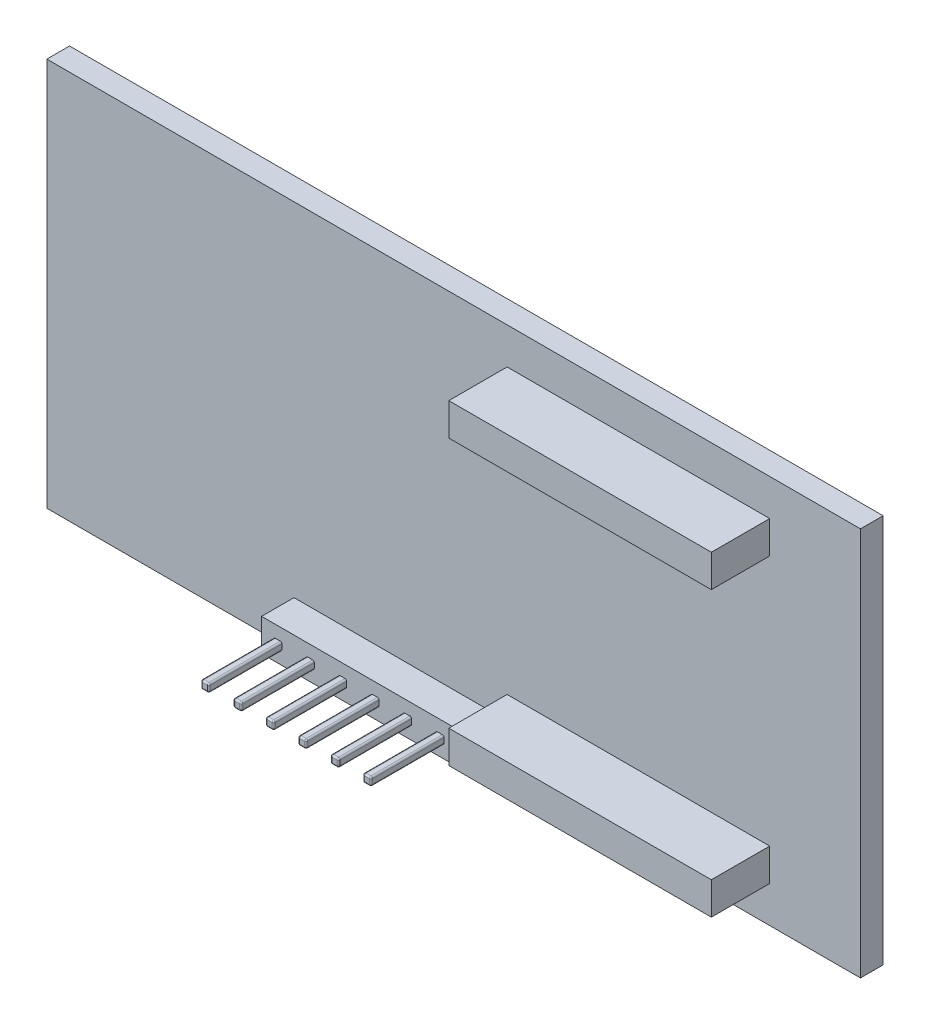
SolidWorks part; units mm, degrees
material "miniBoard"
ref_plane "Front Plane" through (0, 0, 0) normal (0, 0, 1) x (1, 0, 0)
ref_plane "Top Plane" through (0, 0, 0) normal (0, 1, 0) x (1, 0, 0)
ref_plane "Right Plane" through (0, 0, 0) normal (1, 0, 0) x (0, 0, -1)
sketch "Sketch1" plane through (0, 0, 0) normal (0, 0, 1) x (1, 0, 0)
  line L1 (-31.877, 15.24) -> (31.877, 15.24)
  line L2 (-31.877, 15.24) -> (-31.877, -15.24)
  line L3 (-31.877, -15.24) -> (31.877, -15.24)
  line L4 (31.877, 15.24) -> (31.877, -15.24)
  line L5 (-31.877, 15.24) -> (31.877, -15.24) construction
  line L6 (-31.877, -15.24) -> (31.877, 15.24) construction
  point P0 (0, 0)
  dimension "D1" = 30.48
  dimension "D2" = 63.754
extrude "Boss-Extrude1" add sketch "Sketch1" along normal mid plane 1.778
sketch "Sketch2" plane through (0, 0, 0.889) normal (0, 0, 1) x (1, 0, 0)
  line L0 (0, 0) -> (46.4502, 0) construction
  line L1 (24.765, 12.3825) -> (4.191, 12.3825)
  line L2 (24.765, 12.3825) -> (24.765, 9.8425)
  line L3 (24.765, 9.8425) -> (4.191, 9.8425)
  line L4 (4.191, 12.3825) -> (4.191, 9.8425)
  line L5 (24.765, 11.1125) -> (4.191, 11.1125) construction
  line L6 (31.877, -15.24) -> (31.877, 15.24) construction
  dimension "D1" = 11.1125
  dimension "D2" = 20.574
  dimension "D3" = 7.112
  dimension "D4" = 2.54
extrude "Boss-Extrude2" add sketch "Sketch2" along normal blind 4.572
mirror "Mirror1" about plane through (0, 0, 0) normal (0, 1, 0) of "Boss-Extrude2"
sketch "Sketch3" plane through (0, 0, 0.889) normal (0, 0, 1) x (1, 0, 0)
  line L0 (-31.877, -15.24) -> (31.877, -15.24) construction
  line L1 (-10.922, -12.573) -> (-11.557, -12.573)
  line L2 (-10.922, -12.573) -> (-10.922, -13.208)
  line L3 (-10.922, -13.208) -> (-11.557, -13.208)
  line L4 (-11.557, -12.573) -> (-11.557, -13.208)
  line L5 (-31.877, 15.24) -> (-31.877, -15.24) construction
  dimension "D1" = 0.635
  dimension "D2" = 0.635
  dimension "D3" = 2.032
  dimension "D4" = 20.32
extrude "Boss-Extrude3" add sketch "Sketch3" along normal blind 8.255
fillet "Fillet3" radius 0.127 4 edges at (-10.922, -13.208, 5.0165) (-11.557, -13.208, 5.0165) (-10.922, -12.573, 5.0165) (-11.557, -12.573, 5.0165)
fillet "Fillet4" radius 0.127 8 edges at (-11.5198, -13.1708, 9.144) (-11.557, -12.8905, 9.144) (-11.5198, -12.6102, 9.144) (-11.2395, -12.573, 9.144) (-10.9592, -12.6102, 9.144) (-10.922, -12.8905, 9.144) (-10.9592, -13.1708, 9.144) (-11.2395, -13.208, 9.144)
pattern_linear "LPattern1" count 6 spacing 2.54 along (1, 0, 0) of "Boss-Extrude3", "Fillet3", "Fillet4"
sketch "Sketch4" plane through (0, 0, 0.889) normal (0, 0, 1) x (1, 0, 0)
  line L0 (1.778, -12.8905) -> (2.7305, -12.8905) construction
  line L1 (2.7305, -11.6205) -> (-12.5095, -11.6205)
  line L2 (2.7305, -11.6205) -> (2.7305, -14.1605)
  line L3 (2.7305, -14.1605) -> (-12.5095, -14.1605)
  line L4 (-12.5095, -11.6205) -> (-12.5095, -14.1605)
  line L5 (1.778, -13.081) -> (1.778, -12.7) construction
  line L6 (-11.557, -12.8905) -> (-12.5095, -12.8905) construction
  line L8 (-11.557, -12.7) -> (-11.557, -13.081) construction
  dimension "D1" = 2.54
  dimension "D2" = 15.24
extrude "Boss-Extrude4" add sketch "Sketch4" along normal blind 2.54
